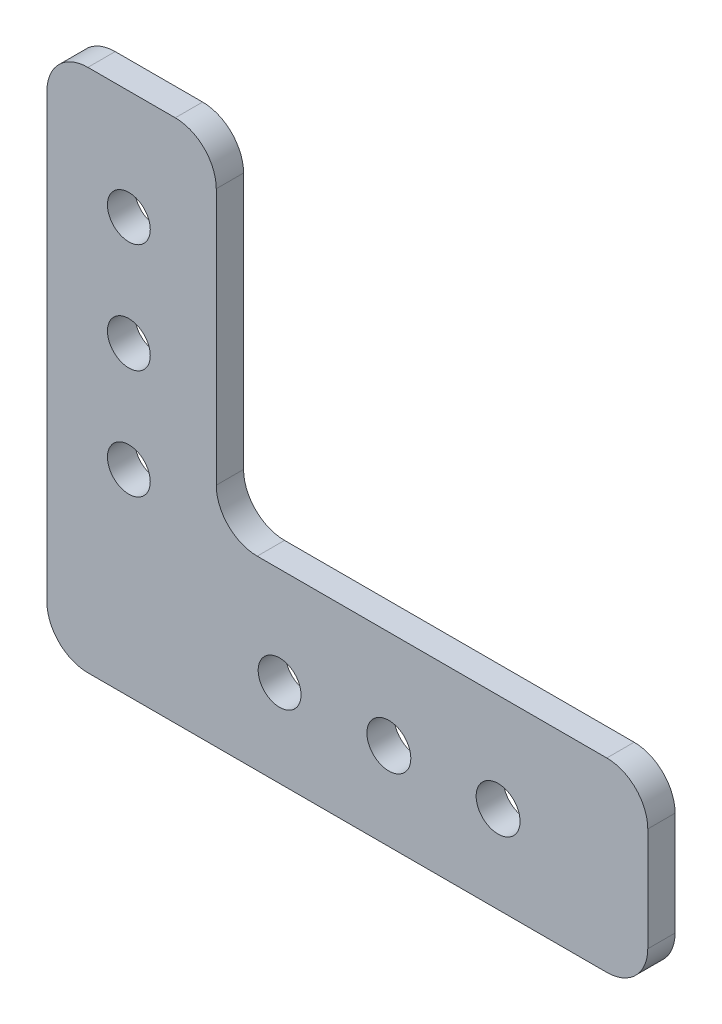
SolidWorks part; units mm, degrees
other "Markup1"
sketch "Sketch3" plane through (-34.925, -29.21, 3.175) normal (0, 0, 1) x (1, 0, 0)
material "6061-T6 (SS)"
ref_plane "Front Plane" through (0, 0, 0) normal (0, 0, 1) x (1, 0, 0)
ref_plane "Top Plane" through (0, 0, 0) normal (0, 1, 0) x (1, 0, 0)
ref_plane "Right Plane" through (0, 0, 0) normal (1, 0, 0) x (0, 0, -1)
sketch "Sketch1" plane through (0, 0, 0) normal (0, 0, 1) x (1, 0, 0)
  line L0 (-10.795, 31.75) -> (-34.925, 31.75) construction
  line L1 (-34.925, -31.75) -> (34.925, -31.75)
  line L2 (-34.925, -31.75) -> (-34.925, 31.75)
  line L3 (-34.925, 31.75) -> (34.925, 31.75)
  line L4 (34.925, -31.75) -> (34.925, 31.75)
  line L5 (-34.925, -31.75) -> (34.925, 31.75) construction
  line L6 (-34.925, 31.75) -> (34.925, -31.75) construction
  line L7 (34.925, 31.75) -> (-10.795, 31.75)
  line L8 (34.925, 31.75) -> (34.925, -7.62)
  line L9 (34.925, -7.62) -> (-10.795, -7.62)
  line L10 (-10.795, 31.75) -> (-10.795, -7.62)
  line L15 (-34.925, -31.75) -> (34.925, -31.75)
  line L16 (-34.925, -31.75) -> (-34.925, -29.21)
  line L17 (-34.925, -29.21) -> (34.925, -29.21)
  line L18 (34.925, -31.75) -> (34.925, -29.21)
  line L19 (-25.4, 31.75) -> (-25.4, -31.75) construction
  circle A0 centre (-25.4, -19.05) radius 2.4892
  circle A1 centre (-25.4, -6.35) radius 2.4892
  circle A2 centre (-25.4, 6.35) radius 2.4892
  circle A3 centre (-25.4, 19.05) radius 2.4892
  circle A4 centre (-7.874, -19.05) radius 2.4892
  circle A5 centre (4.826, -19.05) radius 2.5527
  circle A6 centre (17.526, -19.05) radius 2.5527
  point P0 (0, 0)
  point P31 (0, 0)
  point P32 (0, 0)
  point P33 (0, 0)
  point P34 (0, 0)
  point P35 (0, 0)
  dimension "D7" = 4.9784
  dimension "D1" = 69.85
  dimension "D2" = 63.5
  dimension "D3" = 24.13
  dimension "D4" = 24.13
  dimension "D5" = 27.051
  dimension "D6" = 9.525
  dimension "D11" = 12.7
  dimension "D12" = 12.7
  dimension "D13" = 12.7
  dimension "D15" = 12.7
  dimension "D16" = 2.54
extrude "Boss-Extrude1" add sketch "Sketch1" along normal blind 3.175
sketch "Sketch2" plane through (0, 0, 3.175) normal (0, 0, 1) x (1, 0, 0)
  line L1 (-10.795, 31.75) -> (-15.24, 31.75)
  line L2 (-10.795, 31.75) -> (-10.795, -7.62)
  line L3 (-10.795, -7.62) -> (-15.24, -7.62)
  line L4 (-15.24, 31.75) -> (-15.24, -7.62)
  point P5 (0, 0)
  point P7 (0, 0)
  dimension "D1" = 4.445
extrude "Cut-Extrude1" cut sketch "Sketch2" against normal through all
fillet "Fillet2" radius 4.7625 6 edges at (34.925, -7.62, 1.5875) (34.925, -29.21, 1.5875) (-34.925, 31.75, 1.5875) (-15.24, 31.75, 1.5875) (-15.24, -7.62, 1.5875) (-34.925, -29.21, 1.5875)
